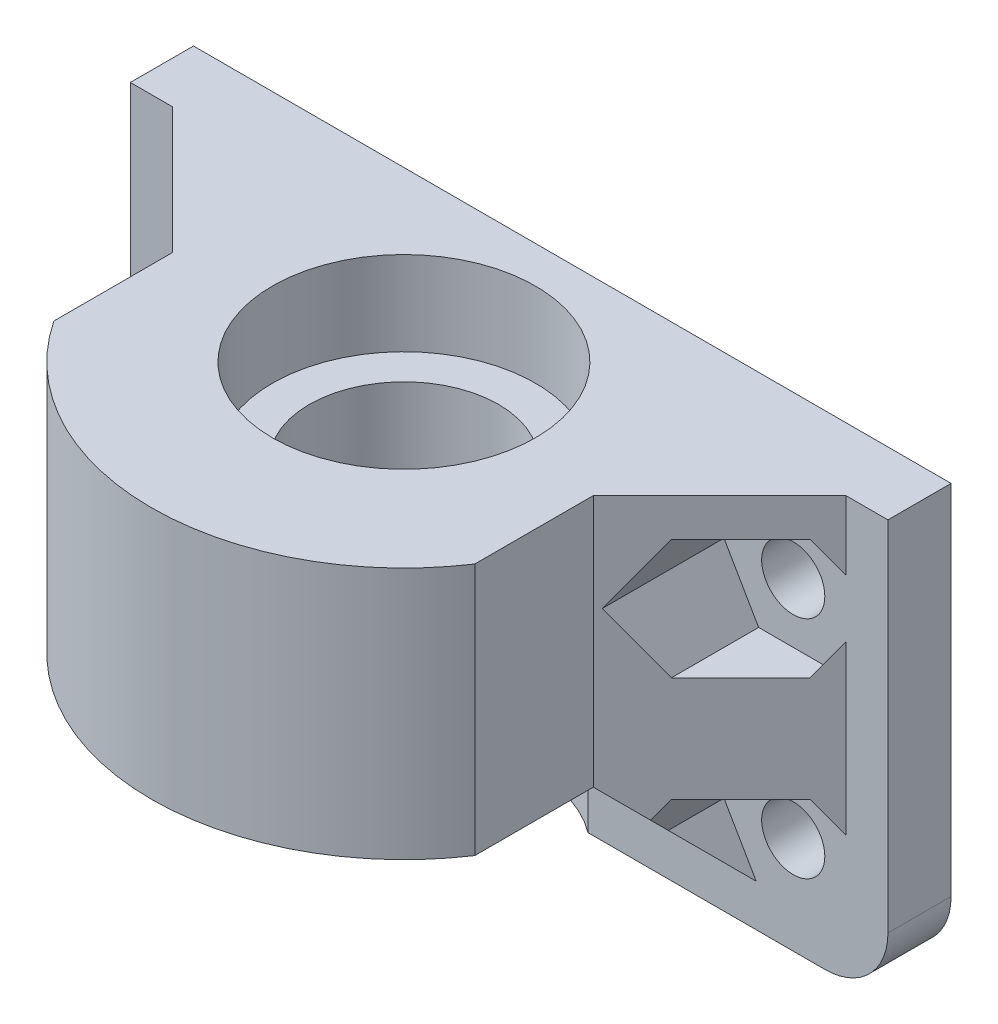
SolidWorks part; units mm, degrees
ref_plane "Front Plane" through (0, 0, 0) normal (0, 0, 1) x (1, 0, 0)
ref_plane "Top Plane" through (0, 0, 0) normal (0, 1, 0) x (1, 0, 0)
ref_plane "Right Plane" through (0, 0, 0) normal (1, 0, 0) x (0, 0, -1)
sketch "Sketch1" plane through (0, 0, 0) normal (0, 0, 1) x (1, 0, 0)
  line L0 (-57.4215, -30) -> (-61.5785, -30) construction
  line L1 (-69.5, -38) -> (-49.5, -38)
  line L2 (-69.5, -38) -> (-69.5, -50)
  line L3 (-69.5, -50) -> (-49.5, -50)
  line L4 (-49.5, -38) -> (-49.5, -50)
  line L5 (-59.5, -33) -> (-59.5, -50) construction
  line L6 (-42, -33) -> (-77, -33) construction
  dimension "D1" = 8
  dimension "D2" = 20
  dimension "D3" = 12
extrude "Boss-Extrude1" add sketch "Sketch1" along normal blind 20
sketch "Sketch2" plane through (0, -50, 0) normal (0, -1, 0) x (1, 0, 0)
  circle A0 centre (-59.5, 8) radius 2 construction
  circle A1 centre (-59.5, 8) radius 2 construction
  circle A2 centre (-59.5, 8) radius 3
  dimension "D1" = 1
extrude "Cut-Extrude1" cut sketch "Sketch2" against normal through all
sketch "Sketch3" plane through (0, -50, 0) normal (0, -1, 0) x (1, 0, 0)
  circle A0 centre (-59.5, 8) radius 6.25
  dimension "D1" = 12.5
extrude "Cut-Extrude2" cut sketch "Sketch3" against normal blind 4
sketch "Sketch4" plane through (0, -46, 0) normal (0, -1, 0) x (1, 0, 0)
  circle A0 centre (-59.5, 8) radius 4.5
  dimension "D1" = 9
extrude "Cut-Extrude3" cut sketch "Sketch4" against normal through all
sketch "Sketch5" plane through (0, -38, 0) normal (0, 1, 0) x (1, 0, 0)
  circle A0 centre (-59.5, -8) radius 6.25 construction
  circle A1 centre (-59.5, -8) radius 6.25
extrude "Cut-Extrude4" cut sketch "Sketch5" against normal blind 4
sketch "Sketch6" plane through (0, 0, 0) normal (0, 0, -1) x (-1, 0, 0)
  line L0 (49.5, -38) -> (41.5, -38)
  line L1 (41.5, -38) -> (41.5, -58)
  line L2 (41.5, -58) -> (77.5, -58)
  line L3 (77.5, -58) -> (77.5, -38)
  line L4 (77.5, -38) -> (69.5, -38)
  line L5 (69.5, -38) -> (69.5, -50)
  line L6 (69.5, -50) -> (49.5, -50)
  line L7 (49.5, -50) -> (49.5, -38)
  dimension "D1" = 8
  dimension "D2" = 20
extrude "Boss-Extrude2" add sketch "Sketch6" against normal blind 3
sketch "Sketch7" plane through (0, -58, 0) normal (0, -1, 0) x (1, 0, 0)
  circle A1 centre (-59.5, 8) radius 6.25
  circle A2 centre (-59.5, 8) radius 6.25
  dimension "D1" = 0
extrude "Cut-Extrude5" cut sketch "Sketch7" against normal up to surface (12 mm away) up to face at (-59.5, -46, 3.5)
chamfer "Chamfer1" distance 6 angle 45 4 edges at (-66.375, -50, 3) (-69.5, -44, 3) (-52.625, -50, 3) (-49.5, -44, 3)
sketch "Sketch8" plane through (0, 0, 3) normal (0, 0, 1) x (1, 0, 0)
  line L0 (-77.5, -42.65) -> (-41.5, -42.65) construction
  line L1 (-77.5, -58) -> (-77.5, -38) construction
  line L2 (-41.5, -38) -> (-41.5, -58) construction
  line L3 (-77.5, -53.35) -> (-41.5, -53.35) construction
  line L4 (-46, -58) -> (-46, -53.35) construction
  line L5 (-41.5, -58) -> (-55.75, -58) construction
  line L6 (-46, -53.35) -> (-46, -42.65) construction
  line L7 (-46, -42.65) -> (-46, -38) construction
  line L8 (-49.5, -38) -> (-43.5, -38) construction
  line L9 (-59.5, -58) -> (-59.5, -38) construction
  line L10 (-47.6454, -39.8) -> (-49.2909, -42.65)
  line L11 (-49.2909, -42.65) -> (-47.6454, -45.5)
  line L12 (-47.6454, -45.5) -> (-44.3546, -45.5)
  line L13 (-44.3546, -45.5) -> (-42.7091, -42.65)
  line L14 (-42.7091, -42.65) -> (-44.3546, -39.8)
  line L15 (-44.3546, -39.8) -> (-47.6454, -39.8)
  line L16 (-47.6454, -50.5) -> (-49.2909, -53.35)
  line L17 (-49.2909, -53.35) -> (-47.6454, -56.2)
  line L18 (-47.6454, -56.2) -> (-44.3546, -56.2)
  line L19 (-44.3546, -56.2) -> (-42.7091, -53.35)
  line L20 (-42.7091, -53.35) -> (-44.3546, -50.5)
  line L21 (-44.3546, -50.5) -> (-47.6454, -50.5)
  line L22 (-63.25, -58) -> (-55.75, -58) construction
  line L23 (-49.5, -38) -> (-69.5, -38) construction
  line L24 (-74.6454, -50.5) -> (-71.3546, -50.5)
  line L25 (-76.2909, -53.35) -> (-74.6454, -50.5)
  line L26 (-74.6454, -56.2) -> (-76.2909, -53.35)
  line L27 (-71.3546, -56.2) -> (-74.6454, -56.2)
  line L28 (-69.7091, -53.35) -> (-71.3546, -56.2)
  line L29 (-71.3546, -50.5) -> (-69.7091, -53.35)
  line L30 (-74.6454, -39.8) -> (-71.3546, -39.8)
  line L31 (-76.2909, -42.65) -> (-74.6454, -39.8)
  line L32 (-74.6454, -45.5) -> (-76.2909, -42.65)
  line L33 (-71.3546, -45.5) -> (-74.6454, -45.5)
  line L34 (-69.7091, -42.65) -> (-71.3546, -45.5)
  line L35 (-71.3546, -39.8) -> (-69.7091, -42.65)
  circle A0 centre (-46, -42.65) radius 2.85 construction
  circle A1 centre (-46, -53.35) radius 2.85 construction
  dimension "D1" = 5.7
  dimension "D2" = 4.5
  dimension "D3" = 1.8
extrude "Cut-Extrude6" cut sketch "Sketch8" along normal blind 14
sketch "Sketch9" plane through (0, 0, 3) normal (0, 0, 1) x (1, 0, 0)
  line L1 (-41.5, -58) -> (-45.2893, -58)
  line L2 (-41.5, -58) -> (-41.5, -53.901)
  line L3 (-41.5, -53.901) -> (-45.2893, -53.901)
  line L4 (-45.2893, -58) -> (-45.2893, -53.901)
  line L5 (-77.5, -58) -> (-73.7107, -58)
  line L6 (-77.5, -58) -> (-77.5, -53.901)
  line L7 (-77.5, -53.901) -> (-73.7107, -53.901)
  line L8 (-73.7107, -58) -> (-73.7107, -53.901)
extrude "Cut-Extrude7" cut sketch "Sketch9" along normal blind 2
sketch "Sketch10" plane through (0, 0, 3) normal (0, 0, 1) x (1, 0, 0)
  line L0 (-74.6454, -39.8) -> (-71.3546, -45.5) construction
  line L1 (-71.3546, -50.5) -> (-74.6454, -56.2) construction
  line L2 (-74.6454, -56.2) -> (-44.3546, -56.2) construction
  line L3 (-44.3546, -56.2) -> (-47.6454, -50.5) construction
  line L4 (-47.6454, -50.5) -> (-47.6454, -45.5) construction
  line L5 (-47.6454, -45.5) -> (-44.3546, -39.8) construction
  line L6 (-47.6454, -50.5) -> (-49.2909, -53.35)
  line L7 (-49.2909, -53.35) -> (-47.6454, -56.2)
  line L8 (-47.6454, -56.2) -> (-44.3546, -56.2)
  line L9 (-44.3546, -56.2) -> (-42.7091, -53.35)
  line L10 (-42.7091, -53.35) -> (-44.3546, -50.5)
  line L11 (-44.3546, -50.5) -> (-47.6454, -50.5)
  line L12 (-47.6454, -50.5) -> (-49.2909, -53.35) construction
  line L13 (-49.2909, -53.35) -> (-47.6454, -56.2) construction
  line L14 (-47.6454, -56.2) -> (-44.3546, -56.2) construction
  line L15 (-44.3546, -56.2) -> (-42.7091, -53.35) construction
  line L16 (-42.7091, -53.35) -> (-44.3546, -50.5) construction
  line L17 (-44.3546, -50.5) -> (-47.6454, -50.5) construction
  line L18 (-47.6454, -39.8) -> (-49.2909, -42.65)
  line L19 (-49.2909, -42.65) -> (-47.6454, -45.5)
  line L20 (-47.6454, -45.5) -> (-44.3546, -45.5)
  line L21 (-44.3546, -45.5) -> (-42.7091, -42.65)
  line L22 (-42.7091, -42.65) -> (-44.3546, -39.8)
  line L23 (-44.3546, -39.8) -> (-47.6454, -39.8)
  line L24 (-47.6454, -39.8) -> (-49.2909, -42.65) construction
  line L25 (-49.2909, -42.65) -> (-47.6454, -45.5) construction
  line L26 (-47.6454, -45.5) -> (-44.3546, -45.5) construction
  line L27 (-44.3546, -45.5) -> (-42.7091, -42.65) construction
  line L28 (-42.7091, -42.65) -> (-44.3546, -39.8) construction
  line L29 (-44.3546, -39.8) -> (-47.6454, -39.8) construction
  line L30 (-71.3546, -39.8) -> (-74.6454, -39.8)
  line L31 (-69.7091, -42.65) -> (-71.3546, -39.8)
  line L32 (-71.3546, -45.5) -> (-69.7091, -42.65)
  line L33 (-74.6454, -45.5) -> (-71.3546, -45.5)
  line L34 (-76.2909, -42.65) -> (-74.6454, -45.5)
  line L35 (-74.6454, -39.8) -> (-76.2909, -42.65)
  line L36 (-71.3546, -39.8) -> (-74.6454, -39.8) construction
  line L37 (-69.7091, -42.65) -> (-71.3546, -39.8) construction
  line L38 (-71.3546, -45.5) -> (-69.7091, -42.65) construction
  line L39 (-74.6454, -45.5) -> (-71.3546, -45.5) construction
  line L40 (-76.2909, -42.65) -> (-74.6454, -45.5) construction
  line L41 (-74.6454, -39.8) -> (-76.2909, -42.65) construction
  line L42 (-71.3546, -50.5) -> (-74.6454, -50.5)
  line L43 (-69.7091, -53.35) -> (-71.3546, -50.5)
  line L44 (-71.3546, -56.2) -> (-69.7091, -53.35)
  line L45 (-74.6454, -56.2) -> (-71.3546, -56.2)
  line L46 (-76.2909, -53.35) -> (-74.6454, -56.2)
  line L47 (-74.6454, -50.5) -> (-76.2909, -53.35)
  line L48 (-71.3546, -50.5) -> (-74.6454, -50.5) construction
  line L49 (-69.7091, -53.35) -> (-71.3546, -50.5) construction
  line L50 (-71.3546, -56.2) -> (-69.7091, -53.35) construction
  line L51 (-74.6454, -56.2) -> (-71.3546, -56.2) construction
  line L52 (-76.2909, -53.35) -> (-74.6454, -56.2) construction
  line L53 (-74.6454, -50.5) -> (-76.2909, -53.35) construction
  arc A0 (-71.3546, -45.5) -> (-71.3546, -50.5) centre (-69.9112, -48) ccw construction
  circle A1 centre (-73, -42.65) radius 1.5
  circle A2 centre (-73, -53.35) radius 1.5
  circle A3 centre (-46, -53.35) radius 1.5
  circle A4 centre (-46, -42.65) radius 1.5
  dimension "D5" = 3
  dimension "D1" = 0
  dimension "D2" = 0
  dimension "D3" = 0
  dimension "D4" = 0
extrude "Cut-Extrude8" cut sketch "Sketch10" against normal through all
sketch "Sketch11" plane through (0, -50, 0) normal (0, -1, 0) x (1, 0, 0)
  line L0 (-69.5, 20) -> (-49.5, 20) construction
  line L1 (-48.4205, -6.7254) -> (-70.5795, -6.7254)
  line L2 (-48.4205, -6.7254) -> (-48.4205, 22.7254)
  line L3 (-48.4205, 22.7254) -> (-70.5795, 22.7254)
  line L4 (-70.5795, -6.7254) -> (-70.5795, 22.7254)
  line L5 (-48.4205, -6.7254) -> (-70.5795, 22.7254) construction
  line L6 (-48.4205, 22.7254) -> (-70.5795, -6.7254) construction
  circle A0 centre (-59.5, 8) radius 12
  line M6 (-69.5, 20) -> (-69.5, 9)
  line M10 (-49.5, 9) -> (-49.5, 20)
  line M11 (-49.5, 20) -> (-69.5, 20)
extrude "Cut-Extrude9" cut sketch "Sketch11" against normal through all contours A0 M11 M6 | A0 M10 M11
fillet "Fillet1" radius 3 2 edges at (-41.5, -58, 1.5) (-77.5, -58, 1.5)
